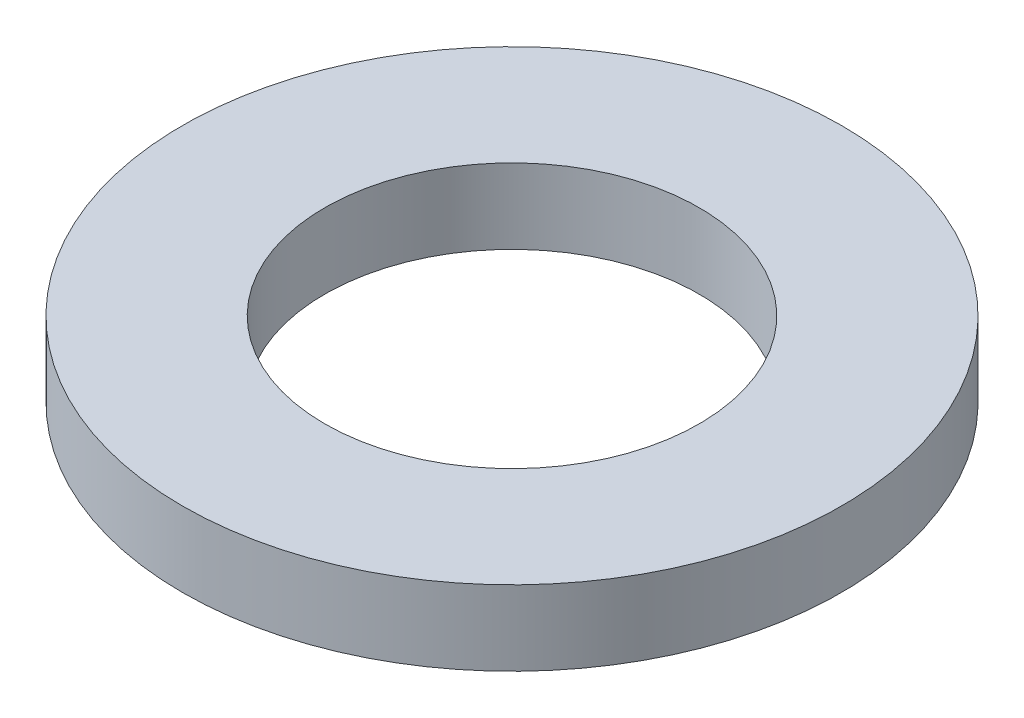
SolidWorks part; units mm, degrees
ref_plane "Alzado" through (0, 0, 0) normal (0, 0, 1) x (1, 0, 0)
ref_plane "Planta" through (0, 0, 0) normal (0, 1, 0) x (1, 0, 0)
ref_plane "Vista lateral" through (0, 0, 0) normal (1, 0, 0) x (0, 0, -1)
sketch "Croquis1" plane through (0, 0, 0) normal (0, 1, 0) x (1, 0, 0)
  circle A0 centre (0, 0) radius 22
  circle A1 centre (0, 0) radius 12.5
  dimension "D1" = 25
  dimension "D2" = 44
extrude "Saliente-Extruir1" add sketch "Croquis1" along normal blind 5
